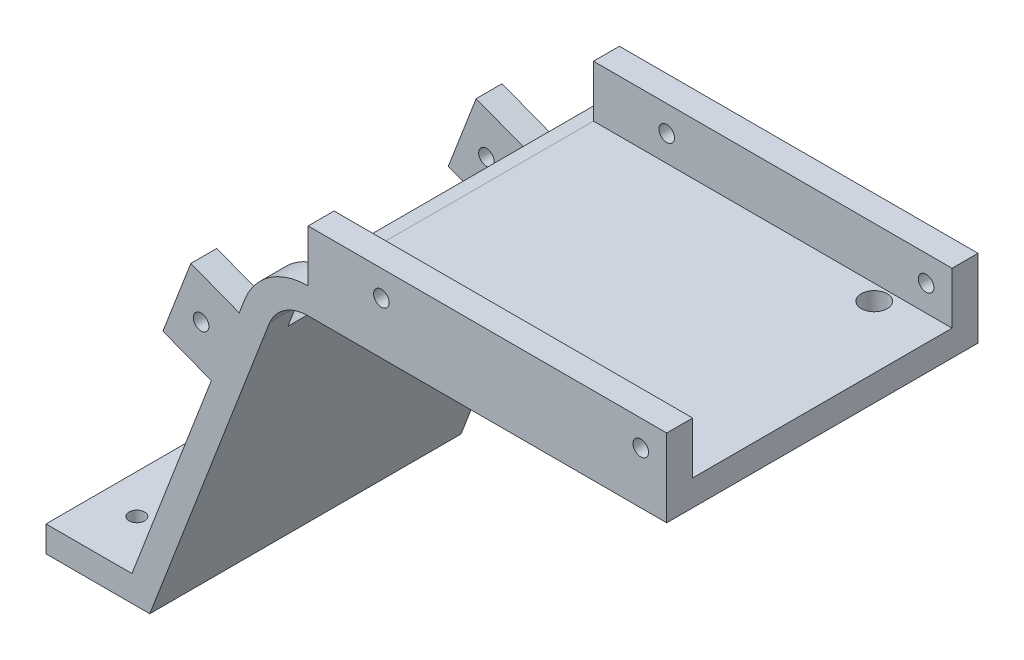
SolidWorks part; units mm, degrees
ref_plane "Front Plane" through (0, 0, 0) normal (0, 0, 1) x (1, 0, 0)
ref_plane "Top Plane" through (0, 0, 0) normal (0, 1, 0) x (1, 0, 0)
ref_plane "Right Plane" through (0, 0, 0) normal (1, 0, 0) x (0, 0, -1)
sketch "Sketch1" plane through (0, 0, 0) normal (0, 0, 1) x (1, 0, 0)
  line L1 (0, 0) -> (120, 0)
  line L2 (0, 0) -> (0, 100)
  line L3 (0, 100) -> (120, 100)
  line L4 (120, 0) -> (120, 100)
  dimension "D1" = 120
  dimension "D2" = 100
extrude "Boss-Extrude1" add sketch "Sketch1" along normal blind 5
sketch "Sketch2" plane through (0, 0, 5) normal (0, 0, 1) x (1, 0, 0)
  line L0 (0, 0) -> (120, 0) construction
  line L3 (85.5794, 7.351) -> (120, 31.4526) construction
  line L4 (120, 0) -> (120, 100) construction
  arc A0 (78.1229, 18) -> (91.9216, 33) centre (50.878, 56.9097) ccw construction
  arc A1 (85.5794, 7.351) -> (103.1546, 26.4563) centre (50.878, 56.9097) ccw
  arc A2 (70.6664, 28.649) -> (80.6886, 39.5437) centre (50.878, 56.9097) ccw
  arc A3 (70.6664, 28.649) -> (85.5794, 7.351) centre (78.1229, 18) ccw
  arc A4 (103.1546, 26.4563) -> (80.6886, 39.5437) centre (91.9216, 33) ccw
  arc A5 (50.878, 9.4097) -> (91.9216, 33) centre (50.878, 56.9097) ccw construction
  arc A6 (50.878, -25.5903) -> (122.1642, 15.3823) centre (50.878, 56.9097) ccw construction
  arc A7 (50.878, 44.4097) -> (61.6789, 50.6177) centre (50.878, 56.9097) ccw construction
  arc A8 (50.878, 44.4097) -> (50.878, -25.5903) centre (50.878, 9.4097) ccw construction
  arc A9 (122.1642, 15.3823) -> (61.6789, 50.6177) centre (91.9216, 33) ccw construction
  circle A10 centre (50.878, 56.9097) radius 2.5
  point P3 (85.8362, 24.7512)
  point P17 (74.548, 15.7274)
  point P27 (115, 5)
  dimension "D1" = 47.5
  dimension "D3" = 13
  dimension "D6" = 5
  dimension "D5" = 35
  dimension "D9" = 5
  dimension "D2" = 15
  dimension "D4" = 33
  dimension "D7" = 5
  dimension "D8" = 35
extrude "Cut-Extrude1" cut sketch "Sketch2" against normal through all
sketch "Sketch3" plane through (0, 0, 0) normal (0, 0, -1) x (-1, 0, 0)
  line L0 (0, 100) -> (0, 0) construction
  line L1 (-120, 0) -> (0, 0)
  line L2 (-120, 0) -> (-120, 1.6)
  line L3 (-120, 1.6) -> (0, 1.6)
  line L4 (0, 0) -> (0, 1.6)
  dimension "D1" = 1.6
extrude "Boss-Extrude2" [suppressed] add sketch "Sketch3" along normal blind 30
sketch "Sketch4" plane through (0, 0, 5) normal (0, 0, 1) x (1, 0, 0)
  line L0 (91.9216, 33) -> (50.878, 56.9097) construction
  line L1 (50.878, 56.9097) -> (78.1229, 18) construction
  line L2 (94.9418, 38.1845) -> (53.8982, 62.0942) construction
  line L3 (54.9738, 59.7776) -> (82.2186, 20.8679) construction
  line L4 (120, 0) -> (120, 100) construction
  line L5 (0, 0) -> (120, 0) construction
  arc A0 (70.2226, 38) -> (73, 50.9665) centre (64.2914, 46.0512) ccw construction
  arc A1 (71.7054, 35.9872) -> (75.1771, 52.1953) centre (64.2914, 46.0512) ccw
  arc A2 (68.7398, 40.0128) -> (70.8229, 49.7377) centre (64.2914, 46.0512) ccw
  arc A3 (68.7398, 40.0128) -> (71.7054, 35.9872) centre (70.2226, 38) ccw
  arc A4 (75.1771, 52.1953) -> (70.8229, 49.7377) centre (73, 50.9665) ccw
  point P13 (74.0696, 43.9567)
  dimension "D3" = 2.5
  dimension "D4" = 10
  dimension "D5" = 47
  dimension "D6" = 38
  dimension "D1" = 6
  dimension "D2" = 5
extrude "Cut-Extrude2" [suppressed] cut sketch "Sketch4" against normal through all
sketch "Sketch5" plane through (0, 0, 5) normal (0, 0, 1) x (1, 0, 0)
  line L0 (120, 70) -> (50.878, 70)
  line L1 (120, 0) -> (120, 100) construction
  line L2 (38.6579, 61.6027) -> (15, 0)
  line L3 (0, 0) -> (120, 0) construction
  line L4 (15, 0) -> (0, 0)
  line L5 (0, 0) -> (0, 100)
  line L6 (0, 100) -> (120, 100)
  line L7 (120, 100) -> (120, 70)
  arc A0 (50.878, 70) -> (38.6579, 61.6027) centre (50.878, 56.9097) ccw
  circle A1 centre (50.878, 56.9097) radius 2.5 construction
  dimension "D1" = 15
  dimension "D2" = 70
extrude "Cut-Extrude3" cut sketch "Sketch5" against normal blind 10
sketch "Sketch7" plane through (0, 0, 0) normal (0, 0, -1) x (-1, 0, 0)
  line L0 (-15, 0) -> (-37.6032, 58.8564)
  line L1 (-120, 70) -> (-50.878, 70)
  line L2 (-120, 70) -> (-120, 65)
  line L3 (-120, 65) -> (-51.317, 65)
  line L5 (-38.6579, 61.6027) -> (-15, 0) construction
  line L7 (-41.98, 56.3067) -> (-20.356, 0)
  line L8 (-15, 0) -> (-120, 0) construction
  line L9 (-20.356, 0) -> (-15, 0)
  line L10 (-91.9216, 33) -> (-50.878, 56.9097) construction
  line L11 (-50.878, 56.9097) -> (-31.4155, 68.2475) construction
  line L12 (-78.1229, 18) -> (-50.878, 56.9097) construction
  line L13 (-50.878, 56.9097) -> (-37.8446, 75.5234) construction
  line L14 (-82.2186, 20.8679) -> (-54.9738, 59.7776) construction
  line L15 (-54.9738, 59.7776) -> (-41.9403, 78.3912) construction
  line L16 (-89.4048, 28.6796) -> (-48.3612, 52.5893) construction
  line L17 (-48.3612, 52.5893) -> (-28.8987, 63.9271) construction
  line L18 (-51.317, 65) -> (-48.0348, 69.6875)
  line L19 (-41.98, 56.3067) -> (-37.6032, 58.8564)
  arc A0 (-50.878, 70) -> (-48.0348, 69.6875) centre (-50.878, 56.9097) cw
  arc A1 (-38.6579, 61.6027) -> (-50.878, 70) centre (-50.878, 56.9097) ccw construction
  dimension "D2" = 5
  dimension "D4" = 5
  dimension "D5" = 5
  dimension "D6" = 5
extrude "Boss-Extrude3" add sketch "Sketch7" along normal blind 60
sketch "Sketch8" plane through (0, 0, -60) normal (0, 0, -1) x (-1, 0, 0)
  line L0 (-20.356, 0) -> (-15, 0) construction
  line L1 (-20.356, 0) -> (-0.356, 0)
  line L2 (-20.356, 0) -> (-20.356, 5)
  line L3 (-20.356, 5) -> (-0.356, 5)
  line L4 (-0.356, 0) -> (-0.356, 5)
  line L5 (-41.98, 56.3067) -> (-20.356, 0) construction
  dimension "D1" = 20
  dimension "D2" = 5
extrude "Boss-Extrude4" add sketch "Sketch8" against normal through all
sketch "Sketch9" plane through (0, 70, 0) normal (0, 1, 0) x (1, 0, 0)
  line L0 (50.878, 60) -> (120, 60) construction
  line L7 (120, 60) -> (120, -5) construction
  circle A0 centre (108, 52) radius 2.5
  dimension "D3" = 5
  dimension "D1" = 8
  dimension "D2" = 12
extrude "Cut-Extrude4" cut sketch "Sketch9" against normal through all
sketch "Sketch10" plane through (0, 0, 0) normal (0, 0, -1) x (-1, 0, 0)
  line L0 (-38.6579, 61.6027) -> (-37.6032, 58.8564)
  line L2 (-43.4829, 60.22) -> (-41.98, 56.3067)
  line L3 (-41.98, 56.3067) -> (-37.6032, 58.8564)
  line L4 (-48.0348, 69.6875) -> (-51.317, 65)
  line L5 (-41.98, 56.3067) -> (-20.356, 0) construction
  arc A0 (-38.6579, 61.6027) -> (-48.0348, 69.6875) centre (-50.878, 56.9097) ccw
  arc A3 (-38.6579, 61.6027) -> (-48.0348, 69.6875) centre (-50.878, 56.9097) ccw construction
  arc A5 (-51.317, 65) -> (-43.4829, 60.22) centre (-50.878, 56.9097) cw
extrude "Boss-Extrude5" add sketch "Sketch10" along normal blind 5
sketch "Sketch11" plane through (120, 0, 0) normal (1, 0, 0) x (0, 0, -1)
  line L0 (-5, 0) -> (0, 0) construction
  line L1 (-5, 0) -> (0, 0)
  line L2 (-5, 0) -> (-5, 70)
  line L3 (-5, 70) -> (0, 70)
  line L4 (0, 0) -> (0, 70)
  line L5 (-5, 0) -> (-5, 70) construction
  line L6 (60, 70) -> (-5, 70) construction
extrude "Cut-Extrude6" cut sketch "Sketch11" against normal through all both and the other way through all
sketch "Sketch12" plane through (0, 5, 0) normal (0, 1, 0) x (1, 0, 0)
  line L0 (0.356, 0) -> (0.356, 60) construction
  line L1 (16.9202, 0) -> (0.356, 0) construction
  line L2 (0.356, 60) -> (16.9202, 60) construction
  circle A0 centre (7.856, 10) radius 1.5
  circle A1 centre (7.856, 50) radius 1.5
  dimension "D1" = 3
  dimension "D2" = 3
  dimension "D5" = 10
  dimension "D3" = 7.5
  dimension "D4" = 10
extrude "Cut-Extrude7" cut sketch "Sketch12" against normal through all both
sketch "Sketch13" plane through (0, 70, 0) normal (0, 1, 0) x (1, 0, 0)
  line L0 (120, 60) -> (120, 0) construction
  line L1 (50.878, 0) -> (120, 0)
  line L2 (50.878, 0) -> (50.878, 5)
  line L3 (50.878, 5) -> (120, 5)
  line L4 (120, 0) -> (120, 5)
  line L6 (50.878, 60) -> (120, 60)
  line L7 (50.878, 60) -> (50.878, 55)
  line L8 (50.878, 55) -> (120, 55)
  line L9 (120, 60) -> (120, 55)
  dimension "D1" = 5
  dimension "D2" = 5
extrude "Boss-Extrude6" add sketch "Sketch13" along normal blind 10
sketch "Sketch14" plane through (0, 0, 0) normal (0, 0, 1) x (1, 0, 0)
  line L1 (50.878, 80) -> (120, 80) construction
  line L2 (120, 80) -> (120, 65) construction
  circle A0 centre (65, 75) radius 1.5
  circle A1 centre (115, 75) radius 1.5
  dimension "D1" = 3
  dimension "D2" = 3
  dimension "D4" = 5
  dimension "D3" = 50
  dimension "D5" = 5
extrude "Cut-Extrude8" cut sketch "Sketch14" against normal through all
sketch "Sketch15" plane through (13.072, -5.0202, 0) normal (-0.9335, 0.3585, 0) x (0, 0, 1)
  line L0 (0, 10.7337) -> (0, 71.367) construction
  line L1 (-5, 68.4251) -> (0, 68.4251)
  line L2 (-5, 68.4251) -> (-5, 53.4251)
  line L3 (-5, 53.4251) -> (0, 53.4251)
  line L4 (0, 68.4251) -> (0, 53.4251)
  line L5 (-60, 68.4251) -> (-55, 68.4251)
  line L6 (-60, 68.4251) -> (-60, 53.4251)
  line L7 (-60, 53.4251) -> (-55, 53.4251)
  line L8 (-55, 68.4251) -> (-55, 53.4251)
  dimension "D1" = 15
extrude "Boss-Extrude7" add sketch "Sketch15" along normal blind 10
sketch "Sketch17" plane through (0, 0, 0) normal (0, 0, 1) x (1, 0, 0)
  line L0 (22.8903, 48.4386) -> (28.2679, 62.4415) construction
  line L1 (22.8903, 48.4386) -> (32.2255, 44.8535) construction
  circle A0 centre (30.2467, 53.6475) radius 1.5
  dimension "D3" = 3
  dimension "D1" = 5
  dimension "D2" = 7.5
extrude "Cut-Extrude9" cut sketch "Sketch17" against normal through all
